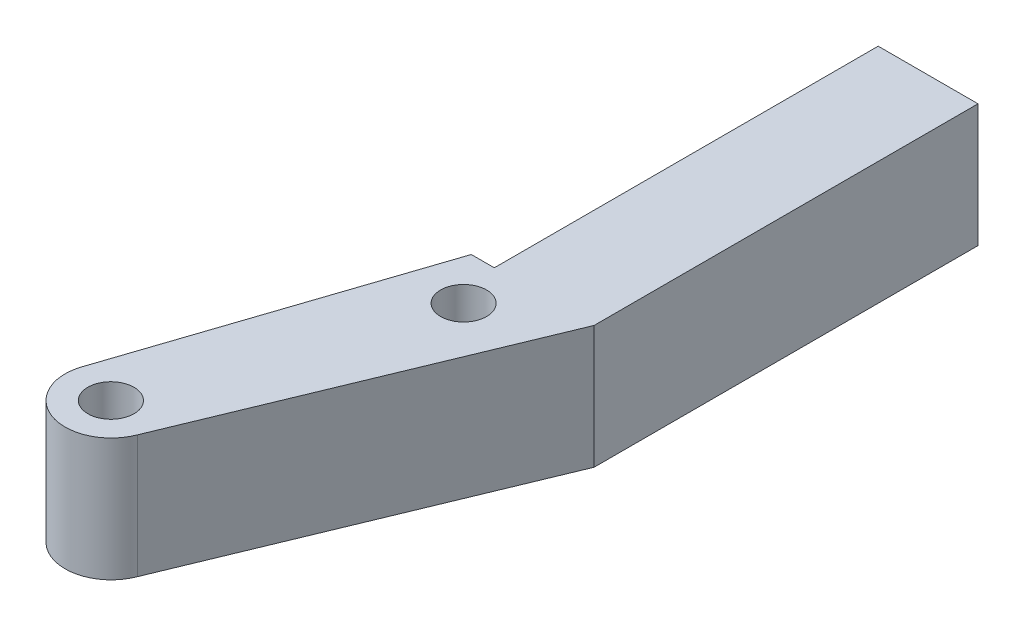
SolidWorks part; units mm, degrees
ref_plane "Alzado" through (0, 0, 0) normal (0, 0, 1) x (1, 0, 0)
ref_plane "Planta" through (0, 0, 0) normal (0, 1, 0) x (1, 0, 0)
ref_plane "Vista lateral" through (0, 0, 0) normal (1, 0, 0) x (0, 0, -1)
sketch "Croquis1" plane through (0, 0, 0) normal (0, 1, 0) x (1, 0, 0)
  line L0 (-1.1976, -21.679) -> (7.4961, -0.6486)
  line L1 (7.4961, -0.6486) -> (7.4961, 24.3514)
  line L2 (7.4961, 24.3514) -> (0.9961, 24.3514)
  line L3 (0.9961, 24.3514) -> (0.9961, -0.6486)
  line L4 (0.9961, -0.6486) -> (-0.5039, -0.6486)
  line L5 (-0.5039, -0.6486) -> (-6.8724, -19.7402)
  circle A0 centre (1.9961, -3.6486) radius 1.5
  circle A1 centre (-4.0039, -20.6186) radius 1.5
  arc A2 (-6.8724, -19.7402) -> (-1.1976, -21.679) centre (-4.0002, -20.6078) ccw
extrude "Saliente-Extruir1" add sketch "Croquis1" along normal blind 8
